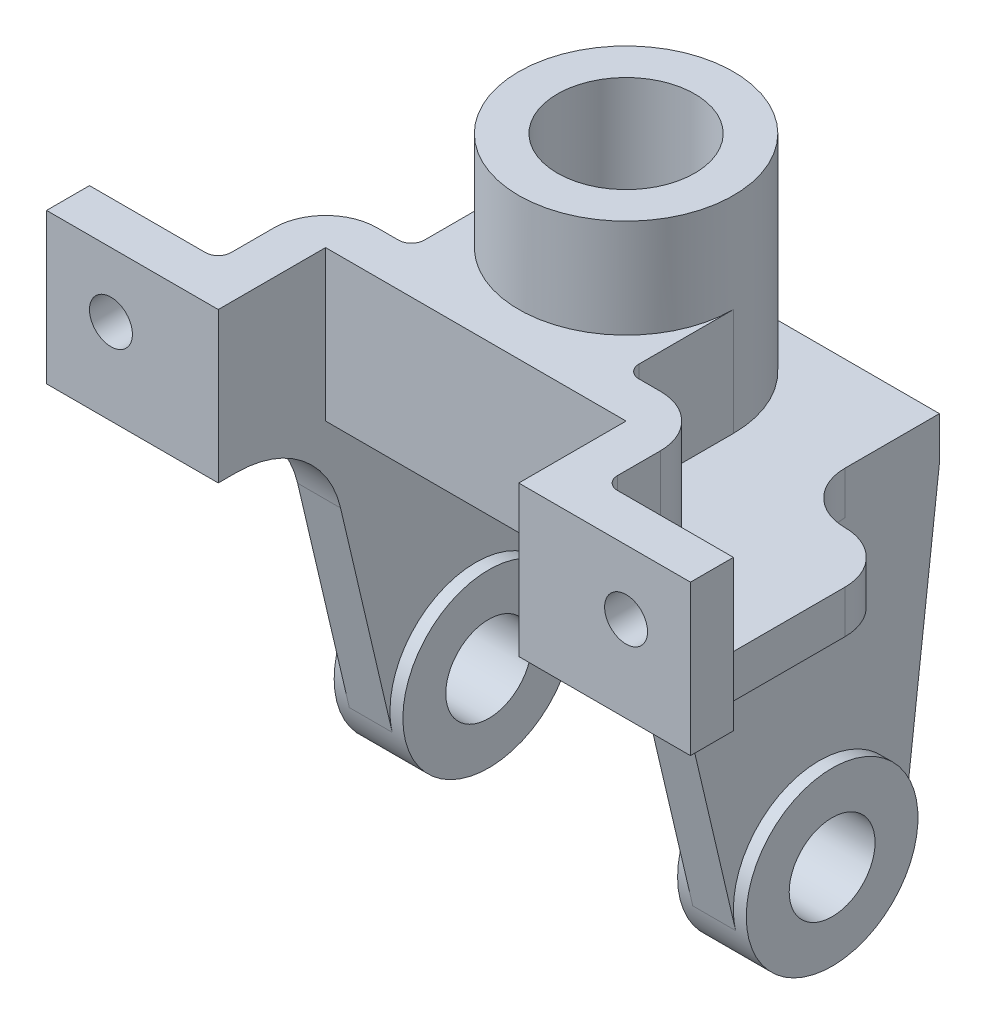
SolidWorks part; units mm, degrees
material "AISI 304"
ref_plane "Front Plane" through (0, 0, 0) normal (0, 0, 1) x (1, 0, 0)
ref_plane "Top Plane" through (0, 0, 0) normal (0, 1, 0) x (1, 0, 0)
ref_plane "Right Plane" through (0, 0, 0) normal (1, 0, 0) x (0, 0, -1)
sketch "Sketch1" plane through (0, 0, 0) normal (0, 1, 0) x (1, 0, 0)
  line L0 (0, 91.892) -> (0, -91.892) construction
  line L2 (-45, 28) -> (45, 28)
  line L3 (45, 28) -> (45, 6)
  line L4 (69, -18) -> (69, -50)
  line L5 (69, -50) -> (75, -50)
  line L6 (75, -50) -> (75, -60)
  line L7 (75, -60) -> (35, -60)
  line L8 (35, -60) -> (35, -35)
  line L9 (35, -35) -> (-35, -35)
  line L10 (-35, -60) -> (-35, -35)
  line L11 (-75, -60) -> (-35, -60)
  line L12 (-75, -50) -> (-75, -60)
  line L13 (-69, -50) -> (-75, -50)
  line L14 (-69, -18) -> (-69, -50)
  line L15 (-45, 28) -> (-45, 6)
  arc A0 (45, 6) -> (57, -6) centre (57, 6) ccw
  arc A1 (57, -6) -> (69, -18) centre (57, -18) cw
  arc A2 (-57, -6) -> (-69, -18) centre (-57, -18) ccw
  arc A3 (-45, 6) -> (-57, -6) centre (-57, 6) cw
  point P4 (0, 0)
  point P8 (0, 0)
  point P27 (0, -35)
  dimension "D6" = 12
  dimension "D1" = 90
  dimension "D2" = 70
  dimension "D3" = 150
  dimension "D4" = 6
  dimension "D5" = 10
  dimension "D7" = 88
  dimension "D8" = 25
  dimension "D9" = 42
  dimension "D10" = 28
extrude "Boss-Extrude1" add sketch "Sketch1" along normal blind 10
sketch "Sketch2" plane through (0, 10, 0) normal (0, 1, 0) x (1, 0, 0)
  circle A0 centre (0, 0) radius 25
  dimension "D2" = 50
extrude "Boss-Extrude2" add sketch "Sketch2" along normal blind 48
sketch "Sketch3" plane through (0, 58, 0) normal (0, 1, 0) x (1, 0, 0)
  circle A0 centre (0, 0) radius 16
  dimension "D1" = 32
extrude "Cut-Extrude1" cut sketch "Sketch3" against normal through all
sketch "Sketch4" plane through (0, 10, 0) normal (0, 1, 0) x (1, 0, 0)
  line L0 (-25, 0) -> (-25, -22)
  line L1 (-28, -25) -> (-33, -25)
  line L2 (-45, -37) -> (-45, -47)
  line L3 (-48, -50) -> (-75, -50)
  line L4 (-75, -50) -> (-75, -60) construction
  line L5 (-69, -50) -> (-75, -50) construction
  line L6 (-75, -50) -> (-75, -60)
  line L7 (-75, -60) -> (-35, -60)
  line L8 (-35, -60) -> (-35, -35)
  line L9 (-35, -60) -> (-35, -35) construction
  line L10 (-35, -35) -> (35, -35)
  line L11 (-35, -35) -> (35, -35) construction
  line L12 (0, 0) -> (0, 96.0496) construction
  line L13 (35, -60) -> (35, -35)
  line L14 (75, -60) -> (35, -60)
  line L15 (75, -50) -> (75, -60)
  line L16 (48, -50) -> (75, -50)
  line L17 (45, -37) -> (45, -47)
  line L18 (28, -25) -> (33, -25)
  line L19 (25, 0) -> (25, -22)
  circle A0 centre (0, 0) radius 25 construction
  circle A1 centre (0, 0) radius 25 construction
  arc A2 (-25, -22) -> (-28, -25) centre (-28, -22) cw
  arc A3 (-33, -25) -> (-45, -37) centre (-33, -37) ccw
  arc A4 (-45, -47) -> (-48, -50) centre (-48, -47) cw
  arc A5 (-25, 0) -> (25, 0) centre (0, 0) ccw
  arc A6 (45, -47) -> (48, -50) centre (48, -47) ccw
  arc A7 (33, -25) -> (45, -37) centre (33, -37) cw
  arc A8 (25, -22) -> (28, -25) centre (28, -22) ccw
  point P44 (0, -35)
  dimension "D1" = 3
  dimension "D2" = 3
  dimension "D3" = 12
  dimension "D4" = 10
  dimension "D5" = 25
extrude "Boss-Extrude3" add sketch "Sketch4" along normal blind 25
sketch "Sketch5" plane through (-45, 0, 0) normal (-1, 0, 0) x (0, 0, 1)
  line L4 (-28, 0) -> (-19.8597, -68.3647)
  line L5 (19.4708, -70.5703) -> (36.0355, 0)
  line L6 (18, 0) -> (50, 0) construction
  line L7 (36.0355, 0) -> (-28, 0)
  line L8 (0, 0) -> (0, -132) construction
  arc A1 (-19.8597, -68.3647) -> (19.4708, -70.5703) centre (0, -66) ccw
  point P12 (0, -66)
  dimension "D1" = 20
  dimension "D2" = 66
  dimension "D3" = 20
extrude "Boss-Extrude5" add sketch "Sketch5" against normal blind 10
ref_plane "Plane2" through (-40, 0, 0) normal (-1, 0, 0) x (0, 0, 1)
sketch "Sketch6" plane through (-40, 0, 0) normal (-1, 0, 0) x (0, 0, 1)
  circle A0 centre (0, -66) radius 20
  arc A1 (-19.8597, -68.3647) -> (19.4708, -70.5703) centre (0, -66) ccw construction
extrude "Boss-Extrude6" add sketch "Sketch6" along normal mid plane 16
sketch "Sketch7" plane through (-48, 0, 0) normal (-1, 0, 0) x (0, 0, 1)
  circle A0 centre (0, -66) radius 10
  dimension "D1" = 20
extrude "Cut-Extrude2" cut sketch "Sketch7" against normal up to next (16 mm away)
fillet "Fillet1" radius 25 1 edges at (-40, 0, 36.0355)
mirror "Mirror1" about plane through (0, 0, 0) normal (1, 0, 0) of "Boss-Extrude5", "Fillet1", "Cut-Extrude2", "Boss-Extrude6"
sketch "Sketch8" plane through (0, 0, 50) normal (0, 0, -1) x (-1, 0, 0)
  line L0 (0, 0) -> (0, 63.3659) construction
  line L1 (-75, 35) -> (-48, 35) construction
  line L2 (-75, 35) -> (-75, 0) construction
  circle A0 centre (-60, 20) radius 5
  circle A1 centre (60, 20) radius 5
  dimension "D1" = 10
  dimension "D2" = 15
  dimension "D3" = 15
extrude "Cut-Extrude3" cut sketch "Sketch8" against normal up to next
